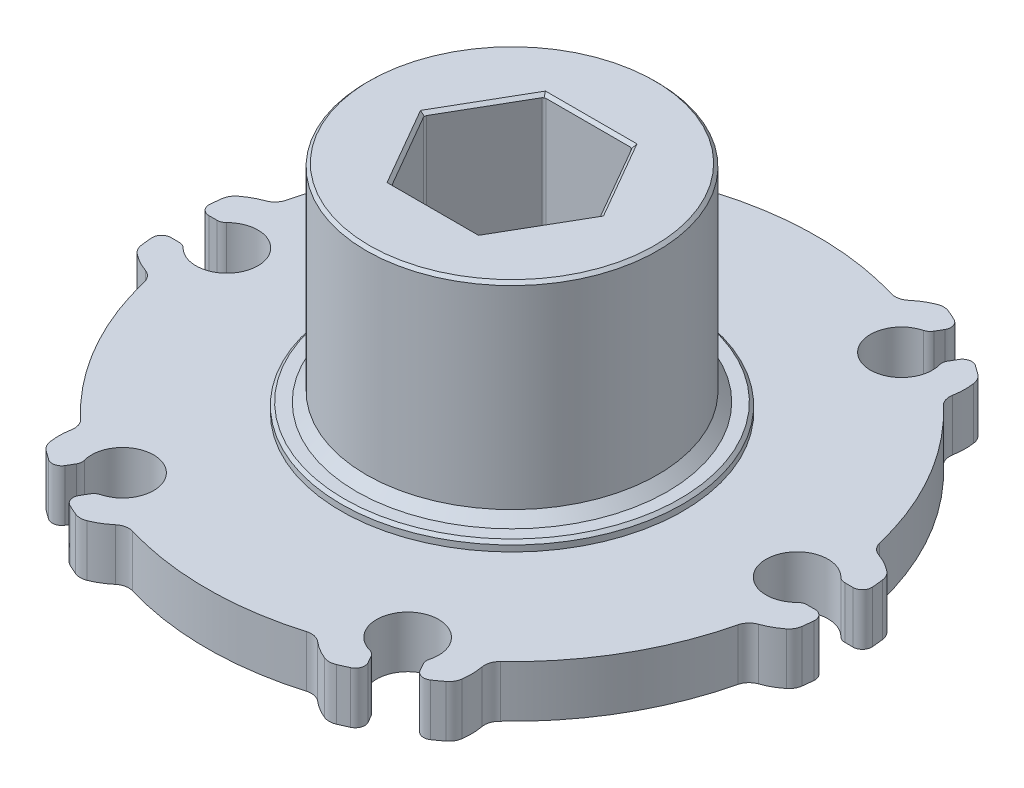
SolidWorks part; units mm, degrees
ref_plane "Front Plane" through (0, 0, 0) normal (0, 0, 1) x (1, 0, 0)
ref_plane "Top Plane" through (0, 0, 0) normal (0, 1, 0) x (1, 0, 0)
ref_plane "Right Plane" through (0, 0, 0) normal (1, 0, 0) x (0, 0, -1)
sketch "Sketch1" plane through (0, 0, 0) normal (0, 1, 0) x (1, 0, 0)
  circle A0 centre (0, 0) radius 27.7876
  dimension "D1" = 55.5752
extrude "Boss-Extrude1" add sketch "Sketch1" along normal blind 8.128
sketch "Sketch6" plane through (0, 8.128, 0) normal (0, 1, 0) x (1, 0, 0)
  line L0 (0, 0) -> (33.6287, 0) construction
  line L2 (25.86, 1.5875) -> (37.4574, 1.5875)
  line L3 (37.4574, 1.5875) -> (37.4574, -1.5875)
  line L4 (25.86, -1.5875) -> (37.4574, -1.5875)
  arc A0 (23.6716, 2.587) -> (23.6716, -2.587) centre (0, 0) ccw
  arc A2 (25.86, 1.5875) -> (25.86, -1.5875) centre (23.8125, 0) ccw
  point P15 (37.4574, 0)
  dimension "D1" = 47.625
  dimension "D2" = 5.1816
  dimension "D3" = 3.175
extrude "Cut-Extrude1" cut sketch "Sketch6" against normal through all
fillet "Fillet4" radius 0.7874 4 edges at (25.86, 4.064, -1.5875) (25.86, 4.064, 1.5875) (27.7422, 4.064, 1.5875) (27.7422, 4.064, -1.5875)
pattern_circular "CirPattern1" count 6 over 360 about axis through (0, 0, 0) along (0, 1, 0) of "Cut-Extrude1", "Fillet4"
sketch "Sketch9" plane through (0, 8.128, 0) normal (0, 1, 0) x (-1, 0, 0)
  circle A0 centre (0, 0) radius 12.1666
  dimension "D1" = 24.3332
extrude "Boss-Extrude2" add sketch "Sketch9" along normal blind 17.272
sketch "Sketch10" plane through (0, 25.4, 0) normal (0, 1, 0) x (1, 0, 0)
  circle A0 centre (0, 0) radius 6.4643
  dimension "D1" = 12.9286
extrude "Cut-Extrude2" cut sketch "Sketch10" against normal through all
sketch "Sketch11" plane through (0, 25.4, 0) normal (0, 1, 0) x (1, 0, 0)
  line L0 (0, 0) -> (17.2829, 0) construction
  line L1 (17.2829, 0) -> (0, 0) construction
  line L2 (0, 0) -> (-19.1344, 0) construction
  line L3 (-8.0518, -1.6573) -> (8.0518, -1.6573)
  line L4 (-8.0518, 1.6573) -> (8.0518, 1.6573)
  line L6 (8.0518, 1.6573) -> (8.0518, -1.6573)
  line L7 (-8.0518, 1.6573) -> (-8.0518, -1.6573)
  line L8 (0, 1.6573) -> (17.2829, 1.6573) construction
  line L9 (0, -1.6573) -> (17.2829, -1.6573) construction
  dimension "D2" = 16.1036
extrude "Cut-Extrude3" cut sketch "Sketch11" against normal through all
chamfer "Chamfer1" distance 0.254 angle 45 5 edges at (0, 0, 6.4643) (0, 0, -6.4643) (0, 25.4, -6.4643) (0, 25.4, 6.4643) (0, 25.4, 12.1666)
fillet "Fillet5" radius 0.127 8 edges at (6.2482, 12.7, 1.6573) (-6.2482, 12.7, 1.6573) (-8.0518, 12.7, 1.6573) (-8.0518, 12.7, -1.6573) (-6.2482, 12.7, -1.6573) (6.2482, 12.7, -1.6573) (8.0518, 12.7, -1.6573) (8.0518, 12.7, 1.6573)
chamfer "Chamfer2" distance 0.8128 angle 45 1 edges at (0, 8.128, 12.1666)
sketch "Sketch12" plane through (0, 0, 0) normal (0, 0, 1) x (1, 0, 0)
  line L0 (-38.1, 7.366) -> (-38.1, 3.048) construction
  line L1 (-38.1, 12.446) -> (-14.2748, 12.446)
  line L2 (-38.1, 12.446) -> (-38.1, 7.366)
  line L3 (-38.1, 7.366) -> (-14.2748, 7.366)
  line L4 (-14.2748, 12.446) -> (-14.2748, 7.366)
  line L5 (-38.1, 3.048) -> (-14.2748, 3.048)
  line L6 (-38.1, 3.048) -> (-38.1, -2.032)
  line L7 (-38.1, -2.032) -> (-14.2875, -2.032)
  line L8 (-14.2748, 3.048) -> (-14.2748, 1.524)
  line L9 (-14.2748, 7.366) -> (-14.2748, 3.048) construction
  line L10 (30.4512, 0) -> (-30.4512, 0) construction
  line L11 (-15.9567, 8.128) -> (-27.6799, 8.128) construction
  line L12 (0, -13.97) -> (0, 13.97) construction
  line L13 (0, -1.0758) -> (0, 10.541) construction
  line L14 (-14.2875, -2.032) -> (-8.89, -2.032)
  line L15 (-8.89, -2.032) -> (-8.89, 1.524)
  line L16 (-8.89, 1.524) -> (-14.2748, 1.524)
  dimension "D1" = 3.048
  dimension "D2" = 0.762
  dimension "D3" = 14.2748
  dimension "D4" = 38.1
  dimension "D5" = 5.08
  dimension "D6" = 5.08
  dimension "D7" = 1.524
  dimension "D8" = 8.89
  dimension "D9" = 4.318
revolve "Cut-Revolve1" cut sketch "Sketch12" angle 360 about L13
chamfer "Chamfer3" distance 0.254 angle 45 2 edges at (0, 8.128, 14.2748) (0, 1.524, -14.2748)
sketch "Sketch13" plane through (0, 25.4, 0) normal (0, 1, 0) x (1, 0, 0)
  circle A0 centre (0, 0) radius 9.2382
extrude "Boss-Extrude3" add sketch "Sketch13" against normal up to surface (25.4 mm away) up to face at (0, 0, 0)
sketch "Sketch14" plane through (0, 25.4, 0) normal (0, 1, 0) x (1, 0, 0)
  line L1 (7.347, 0) -> (3.6735, 6.3627)
  line L2 (3.6735, 6.3627) -> (-3.6735, 6.3627)
  line L3 (-3.6735, 6.3627) -> (-7.347, 0)
  line L4 (-7.347, 0) -> (-3.6735, -6.3627)
  line L5 (-3.6735, -6.3627) -> (3.6735, -6.3627)
  line L6 (3.6735, -6.3627) -> (7.347, 0)
  circle A0 centre (0, 0) radius 6.3627 construction
  dimension "D1" = 12.7254
extrude "Cut-Extrude4" cut sketch "Sketch14" against normal through all
chamfer "Chamfer4" distance 0.254 angle 45 12 edges at (0, 0, 6.3627) (-5.5103, 0, 3.1813) (-5.5103, 0, -3.1813) (0, 0, -6.3627) (5.5103, 0, 3.1813) (5.5103, 0, -3.1814) (5.5103, 25.4, -3.1814) (5.5103, 25.4, 3.1813) (0, 25.4, 6.3627) (-5.5103, 25.4, 3.1813) (-5.5103, 25.4, -3.1813) (0, 25.4, -6.3627)
sketch "Sketch15" plane through (0, 0, 0) normal (0, -1, 0) x (1, 0, 0)
  arc A0 (-17.528, 18.5055) -> (-24.7902, 5.9269) centre (0, 0) ccw
  arc A1 (-25.5999, 5.0256) -> (-28.4538, 2.6286) centre (-23.8125, 0) ccw
  arc A2 (-16.5033, 23.3275) -> (-17.1522, 19.6573) centre (-11.9062, 20.6222) ccw
  arc A3 (-16.5033, 23.3275) -> (-28.4538, 2.6286) centre (0, 0) ccw
  arc A4 (-17.528, 18.5055) -> (-17.1522, 19.6573) centre (-18.4013, 19.4276) ccw
  arc A5 (-24.7902, 5.9269) -> (-25.5999, 5.0256) centre (-26.0254, 6.2222) cw
  dimension "D1" = 50.9778
  dimension "D2" = 10.668
  dimension "D3" = 57.15
  dimension "D4" = 1.27
extrude "Cut-Extrude5" cut sketch "Sketch15" against normal through all
pattern_circular "CirPattern2" count 6 over 360 about axis through (0, 0, 0) along (0, 1, 0) of "Cut-Extrude5"
fillet "Fillet6" radius 1.27 12 edges at (-17.0804, 5.207, 21.9183) (-27.522, 5.207, 3.8329) (-27.522, 5.207, -3.8329) (-17.0804, 5.207, -21.9183) (-10.4416, 5.207, -25.7512) (10.4416, 5.207, -25.7512) (17.0804, 5.207, -21.9183) (27.522, 5.207, -3.8329) (27.522, 5.207, 3.8329) (17.0804, 5.207, 21.9183) (10.4416, 5.207, 25.7512) (-10.4416, 5.207, 25.7512)
chamfer "Chamfer5" distance 0.254 angle 45 1 edges at (0, 0, 9.2382)
fillet "Fillet7" radius 0.254 6 edges at (7.347, 12.7, 0) (3.6735, 12.7, 6.3627) (-3.6735, 12.7, 6.3627) (-7.347, 12.7, 0) (-3.6735, 12.7, -6.3627) (3.6735, 12.7, -6.3627)
